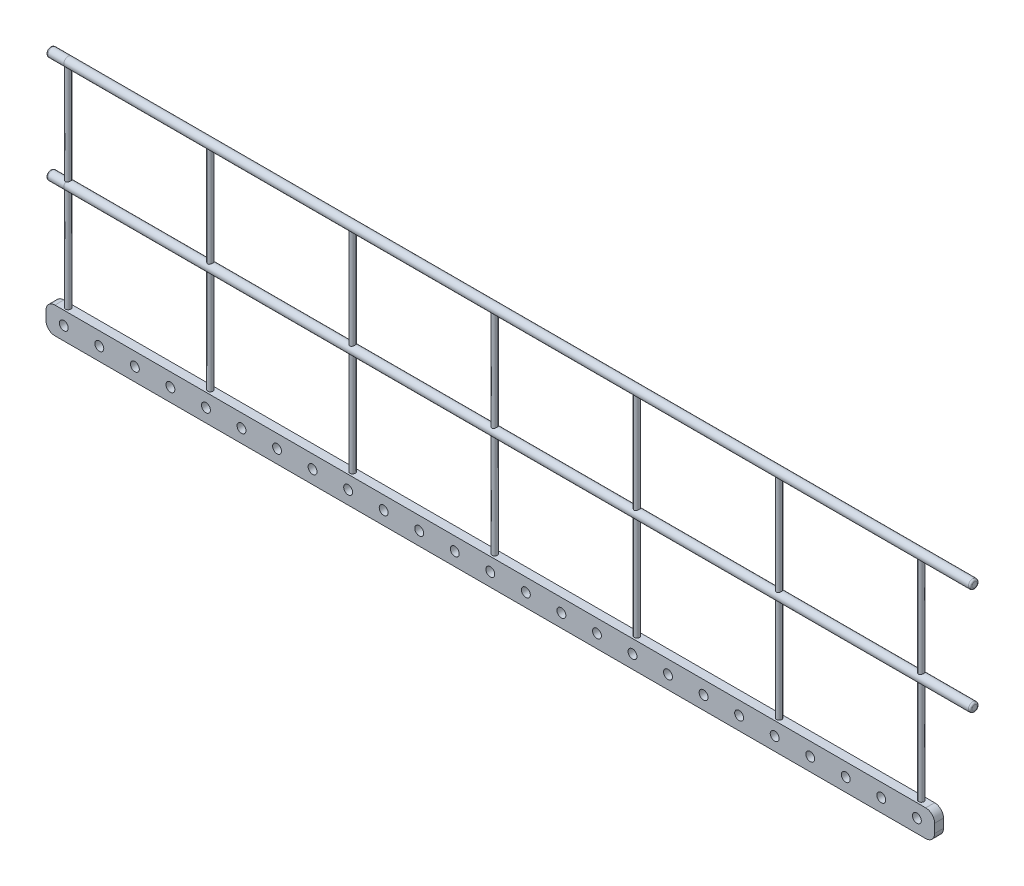
SolidWorks part; units mm, degrees
ref_plane "Front Plane" through (0, 0, 0) normal (0, 0, 1) x (1, 0, 0)
ref_plane "Top Plane" through (0, 0, 0) normal (0, 1, 0) x (1, 0, 0)
ref_plane "Right Plane" through (0, 0, 0) normal (1, 0, 0) x (0, 0, -1)
sketch "Sketch2" plane through (0, 0, 0) normal (0, 0, 1) x (1, 0, 0)
  line L1 (-2500, 75) -> (2500, 75)
  line L2 (-2500, 75) -> (-2500, -75)
  line L3 (-2500, -75) -> (2500, -75)
  line L4 (2500, 75) -> (2500, -75)
  line L5 (-2500, 75) -> (2500, -75) construction
  line L6 (-2500, -75) -> (2500, 75) construction
  point P0 (0, 0)
  dimension "D1" = 5000
  dimension "D2" = 150
extrude "Boss-Extrude1" add sketch "Sketch2" along normal blind 50
fillet "Fillet1" radius 50 4 edges at (-2500, -75, 25) (-2500, 75, 25) (2500, -75, 25) (2500, 75, 25)
sketch "Sketch3" plane through (0, 0, 50) normal (0, 0, 1) x (1, 0, 0)
  line L0 (-2500, 0) -> (-2400, 0) construction
  line L1 (-2500, 25) -> (-2500, -25) construction
  circle A0 centre (-2400, 0) radius 25
  dimension "D2" = 50
  dimension "D1" = 100
extrude "Cut-Extrude1" cut sketch "Sketch3" against normal through all
pattern_linear "LPattern1" count 25 spacing 200 along (1, 0, 0) of "Cut-Extrude1"
sketch "Sketch4" plane through (0, 75, 0) normal (0, 1, 0) x (1, 0, 0)
  line L0 (-2450, -25) -> (-2400, -25) construction
  line L1 (-2450, 0) -> (-2450, -50) construction
  circle A0 centre (-2400, -25) radius 15
  dimension "D2" = 30
  dimension "D1" = 50
extrude "Boss-Extrude2" add sketch "Sketch4" along normal blind 600
pattern_linear "LPattern2" count 10 spacing 800 along (1, 0, 0) of "Boss-Extrude2"
sketch "Sketch5" plane through (0, 675, 0) normal (0, 1, 0) x (1, 0, 0)
  line L0 (-2400, -25) -> (-2500, -25)
  line L1 (-2500, -50) -> (-2500, 0) construction
  line L2 (-2400, -25) -> (2700, -25)
  dimension "D1" = 5100
sweep "Sweep1" add path "Sketch5" circular profile diameter 50 parameters "D3"=50
fillet "Fillet2" radius 10 2 edges at (2700, 675, 50) (-2500, 675, 50)
pattern_linear "LPattern3" count 2 spacing 600 along (0, 1, 0) of "Boss-Extrude2", "LPattern2", "Sweep1", "Fillet2"
